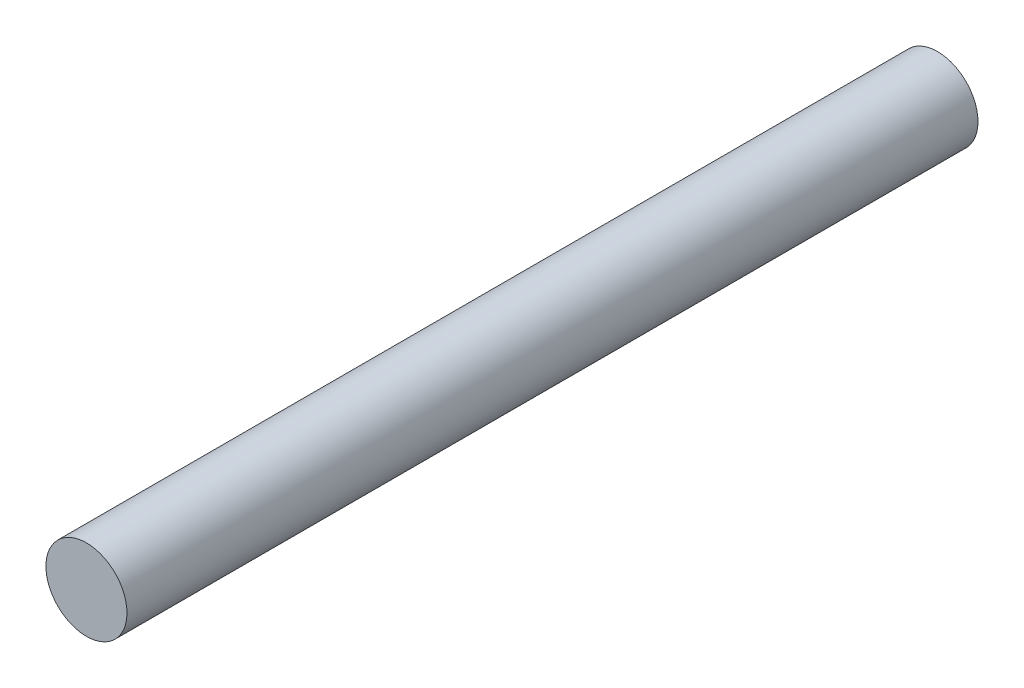
SolidWorks part; units mm, degrees
ref_plane "Front Plane" through (0, 0, 0) normal (0, 0, 1) x (1, 0, 0)
ref_plane "Top Plane" through (0, 0, 0) normal (0, 1, 0) x (1, 0, 0)
ref_plane "Right Plane" through (0, 0, 0) normal (1, 0, 0) x (0, 0, -1)
sketch "Sketch1" plane through (0, 0, 0) normal (0, 0, 1) x (1, 0, 0)
  circle A0 centre (0, -1.0857) radius 12.7
extrude "Boss-Extrude1" add sketch "Sketch1" along normal blind 266.7
